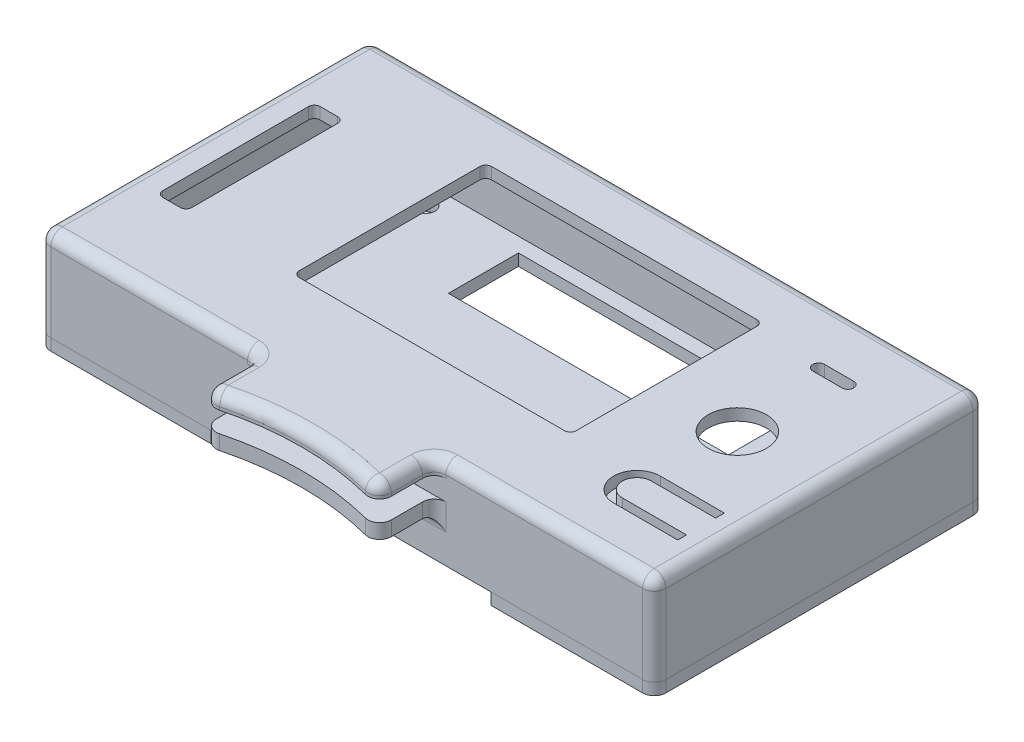
SolidWorks part; units mm, degrees
ref_plane "Alzado" through (0, 0, 0) normal (0, 0, 1) x (1, 0, 0)
ref_plane "Planta" through (0, 0, 0) normal (0, 1, 0) x (1, 0, 0)
ref_plane "Vista lateral" through (0, 0, 0) normal (1, 0, 0) x (0, 0, -1)
sketch "Croquis1" plane through (0, 0, 0) normal (0, 1, 0) x (1, 0, 0)
  line L0 (-2.25, 54.45) -> (103.25, 54.45)
  line L1 (0, 0) -> (101, 0) construction
  line L2 (0, 0) -> (0, 52.2) construction
  line L3 (0, 52.2) -> (101, 52.2) construction
  line L4 (101, 0) -> (101, 52.2) construction
  line L5 (26.6, 45.5) -> (74.1, 45.5)
  line L6 (26.6, 45.5) -> (26.6, 12.5)
  line L7 (26.6, 12.5) -> (74.1, 12.5)
  line L8 (74.1, 45.5) -> (74.1, 12.5)
  line L9 (3, 39.7) -> (8, 39.7)
  line L10 (3, 39.7) -> (3, 12.7)
  line L11 (3, 12.7) -> (8, 12.7)
  line L12 (8, 39.7) -> (8, 12.7)
  line L13 (103.25, -2.25) -> (103.25, 54.45)
  line L14 (-2.25, -2.25) -> (103.25, -2.25)
  line L15 (-2.25, -2.25) -> (-2.25, 54.45)
  line L16 (88.05, 12.48) -> (99.05, 12.48)
  line L17 (88.05, 7.48) -> (99.05, 7.48)
  line L18 (88.05, 5.98) -> (99.05, 5.98)
  line L19 (88.05, 13.98) -> (99.05, 13.98)
  line L20 (99.05, 13.98) -> (99.05, 12.48)
  line L21 (99.05, 7.48) -> (99.05, 5.98)
  line L22 (90.55, 43.65) -> (85.55, 43.65) construction
  line L23 (90.55, 42.65) -> (85.55, 42.65)
  line L24 (90.55, 44.65) -> (85.55, 44.65)
  line L25 (-0.75, -0.75) -> (101.75, -0.75) construction
  line L26 (101.75, -0.75) -> (101.75, 52.95) construction
  line L27 (-0.75, 52.95) -> (101.75, 52.95) construction
  line L28 (-0.75, -0.75) -> (-0.75, 52.95) construction
  circle A0 centre (98.3, 49.5) radius 1.6 construction
  circle A1 centre (98.3, 2.7) radius 1.6 construction
  circle A2 centre (12.3, 49.5) radius 1.6 construction
  circle A3 centre (12.3, 2.7) radius 1.6 construction
  circle A4 centre (88.05, 27.2) radius 5
  circle A5 centre (88.05, 43.65) radius 3 construction
  arc A6 (88.05, 12.48) -> (88.05, 7.48) centre (88.05, 9.98) ccw
  arc A7 (88.05, 13.98) -> (88.05, 5.98) centre (88.05, 9.98) ccw
  arc A8 (90.55, 42.65) -> (90.55, 44.65) centre (90.55, 43.65) ccw
  arc A9 (85.55, 44.65) -> (85.55, 42.65) centre (85.55, 43.65) ccw
  point P41 (88.05, 43.65)
  dimension "D3" = 3.2
  dimension "D6" = 2.7
  dimension "D12" = 10
  dimension "D15" = 6
  dimension "D17" = 5
  dimension "D1" = 52.2
  dimension "D2" = 101
  dimension "D4" = 46.8
  dimension "D5" = 2.7
  dimension "D7" = 86
  dimension "D8" = 47.5
  dimension "D9" = 33
  dimension "D10" = 12.5
  dimension "D11" = 26.9
  dimension "D13" = 12.95
  dimension "D14" = 25
  dimension "D16" = 8.55
  dimension "D18" = 17.22
  dimension "D19" = 27
  dimension "D20" = 5
  dimension "D21" = 12.5
  dimension "D22" = 8
  dimension "D24" = 11
  dimension "D25" = 1.5
  dimension "D26" = 5
  dimension "D27" = 2
  dimension "D23" = 1.5
  dimension "D28" = 0.75
extrude "Saliente-Extruir1" add sketch "Croquis1" along normal blind 2
sketch "Croquis5" plane through (0, 0, 0) normal (0, -1, 0) x (1, 0, 0)
  line L8 (-2.25, 2.25) -> (-2.25, -54.45) construction
  line L9 (-2.25, 2.25) -> (103.25, 2.25) construction
  line L10 (103.25, 2.25) -> (103.25, -54.45) construction
  line L11 (-2.25, -54.45) -> (103.25, -54.45) construction
  line L12 (-2.25, 2.25) -> (-2.25, -54.45)
  line L13 (-2.25, 2.25) -> (103.25, 2.25)
  line L14 (103.25, 2.25) -> (103.25, -54.45)
  line L15 (-2.25, -54.45) -> (103.25, -54.45)
  line L16 (101.75, 0.75) -> (101.75, -52.95) construction
  line L17 (-0.75, 0.75) -> (101.75, 0.75) construction
  line L18 (-0.75, 0.75) -> (-0.75, -52.95) construction
  line L19 (-0.75, -52.95) -> (101.75, -52.95) construction
  line L20 (101.75, 0.75) -> (101.75, -52.95)
  line L21 (-0.75, 0.75) -> (101.75, 0.75)
  line L22 (-0.75, 0.75) -> (-0.75, -52.95)
  line L23 (-0.75, -52.95) -> (101.75, -52.95)
extrude "Saliente-Extruir4" add sketch "Croquis5" along normal blind 13.5
sketch "Croquis6" plane through (0, -13.5, 0) normal (0, -1, 0) x (1, 0, 0)
  line L0 (103.25, 2.25) -> (103.25, -54.45) construction
  line L1 (-2.25, 2.25) -> (103.25, 2.25) construction
  line L2 (-2.25, 2.25) -> (-2.25, -54.45) construction
  line L3 (-2.25, -54.45) -> (103.25, -54.45) construction
  line L4 (103.25, 2.25) -> (103.25, -54.45)
  line L5 (-2.25, 2.25) -> (27.25, 2.25)
  line L6 (-2.25, 2.25) -> (-2.25, -54.45)
  line L7 (-2.25, -54.45) -> (103.25, -54.45)
  line L8 (50.5, 2.25) -> (50.5, -54.45) construction
  line L9 (-0.75, 0.75) -> (-0.75, -52.95) construction
  line L14 (9.45, -48.95) -> (2.45, -48.95)
  line L15 (9.45, -48.95) -> (9.45, -3.95)
  line L16 (9.45, -3.95) -> (2.45, -3.95)
  line L17 (2.45, -48.95) -> (2.45, -3.95)
  line L18 (-0.75, -52.95) -> (101.75, -52.95) construction
  line L19 (103.25, -26.1) -> (-2.25, -26.1) construction
  line L20 (75.25, -50.45) -> (27.25, -50.45)
  line L21 (75.25, -50.45) -> (75.25, -38.45)
  line L22 (75.25, -38.45) -> (27.25, -38.45)
  line L23 (27.25, -50.45) -> (27.25, -38.45)
  line L25 (75.25, 2.25) -> (75.25, -3.75)
  line L26 (75.25, -3.75) -> (27.25, -3.75)
  line L27 (27.25, 2.25) -> (27.25, -3.75)
  line L28 (75.25, 2.25) -> (103.25, 2.25)
  circle A0 centre (98.3, -2.7) radius 1.6 construction
  circle A1 centre (12.3, -49.5) radius 1.6 construction
  circle A2 centre (12.3, -49.5) radius 1.6
  circle A3 centre (98.3, -49.5) radius 1.6 construction
  circle A4 centre (98.3, -2.7) radius 1.6
  circle A7 centre (98.3, -49.5) radius 1.6
  circle A14 centre (12.3, -2.7) radius 1.6 construction
  circle A15 centre (12.3, -2.7) radius 1.6
  circle A16 centre (80.5, -26.1) radius 1.55
  circle A17 centre (20.5, -26.1) radius 1.55
  dimension "D5" = 48
  dimension "D11" = 3.1
  dimension "D1" = 45
  dimension "D2" = 7
  dimension "D3" = 3.2
  dimension "D4" = 4
  dimension "D6" = 12
  dimension "D7" = 2.5
  dimension "D8" = 28
  dimension "D9" = 48
  dimension "D10" = 6
  dimension "D12" = 30
extrude "Saliente-Extruir5" add sketch "Croquis6" along normal blind 2
ref_plane "Plano1" through (0, -13.5, 0) normal (0, -1, 0) x (-1, 0, 0)
sketch "Croquis8" plane through (0, 0, 0) normal (0, -1, 0) x (1, 0, 0)
  line L0 (0, 0) -> (101, 0) construction
  line L2 (9.225, 0.75) -> (9.225, -6.25)
  line L3 (9.225, -6.25) -> (15.375, -6.25)
  line L4 (15.375, 0.75) -> (15.375, -6.25)
  line L5 (101, -26.1) -> (-2.25, -26.1) construction
  line L6 (101, 0) -> (101, -52.2) construction
  line L7 (-2.25, 2.25) -> (-2.25, -54.45) construction
  line L8 (50.5, 0) -> (50.5, -52.2) construction
  line L9 (0, -52.2) -> (101, -52.2) construction
  line L17 (101.75, -6.25) -> (95.6, -6.25)
  line L18 (95.6, 0.75) -> (95.6, -6.25)
  line L23 (101.75, 0.75) -> (101.75, -52.95) construction
  line L24 (-0.75, 0.75) -> (101.75, 0.75) construction
  line L25 (95.6, 0.75) -> (101.75, 0.75)
  line L26 (101.75, 0.75) -> (101.75, -6.25)
  line L27 (9.225, 0.75) -> (15.375, 0.75)
  line L28 (9.225, -52.95) -> (15.375, -52.95)
  line L29 (15.375, -52.95) -> (15.375, -45.95)
  line L30 (9.225, -45.95) -> (15.375, -45.95)
  line L31 (9.225, -52.95) -> (9.225, -45.95)
  line L32 (101.75, -52.95) -> (101.75, -45.95)
  line L33 (95.6, -52.95) -> (101.75, -52.95)
  line L34 (101.75, -45.95) -> (95.6, -45.95)
  line L35 (95.6, -52.95) -> (95.6, -45.95)
  dimension "D1" = 6.15
  dimension "D2" = 7
  dimension "D3" = 3.075
  dimension "D4" = 7
  dimension "D5" = 6.15
extrude "Saliente-Extruir13" add sketch "Croquis8" along normal blind 9
sketch "Croquis9" plane through (0, -9, 0) normal (0, -1, 0) x (1, 0, 0)
  circle A0 centre (12.3, -2.7) radius 2.15
  circle A1 centre (98.3, -2.7) radius 2.15
  circle A2 centre (98.3, -49.5) radius 2.15
  circle A3 centre (12.3, -49.5) radius 2.15
  dimension "D1" = 4.3
extrude "Cortar-Extruir2" cut sketch "Croquis9" against normal blind 3.5
split "Partir1" trim tools "Plano1" bodies to split 108 resulting bodies 111 112
fillet "Redondeo6" radius 1 8 edges at (8, 1, -39.7) (3, 1, -39.7) (3, 1, -12.7) (8, 1, -12.7) (26.6, 1, -12.5) (74.1, 1, -12.5) (74.1, 1, -45.5) (26.6, 1, -45.5)
fillet "Redondeo7" radius 1 18 edges at (101.75, -4.5, -6.25) (100.4, 0, -6.25) (95.6, 0, -2.615) (95.6, -4.5, 0.75) (9.225, -4.5, 0.75) (9.225, 0, -2.75) (12.3, 0, -6.25) (15.375, 0, -2.75) (15.375, -4.5, 0.75) (9.225, -4.5, -52.95) (9.225, 0, -49.45) (12.3, 0, -45.95) (15.375, 0, -49.45) (15.375, -4.5, -52.95) (95.6, -4.5, -52.95) (101.75, -4.5, -45.95) (98.675, 0, -45.95) (95.6, 0, -49.45)
sketch "Croquis10" plane through (0, 0, 0) normal (0, -1, 0) x (1, 0, 0)
  circle A0 centre (88.05, -9.98) radius 2.5
extrude "Saliente-Extruir14" add sketch "Croquis10" along normal blind 2 contours A0
sketch "Croquis13" plane through (0, 0, 2.25) normal (0, 0, 1) x (1, 0, 0)
  line L0 (50.5, 2) -> (50.5, -13.5) construction
  line L1 (-2.25, 2) -> (103.25, 2) construction
  line L2 (103.25, -13.5) -> (-2.25, -13.5) construction
  line L4 (35.5, 2) -> (65.5, 2)
  line L5 (35.5, 2) -> (35.5, -0.5)
  line L6 (35.5, -0.5) -> (65.5, -0.5)
  line L7 (65.5, 2) -> (65.5, -0.5)
  line L8 (35.5, -4) -> (65.5, -4)
  line L9 (35.5, -4) -> (35.5, -6.5)
  line L10 (35.5, -6.5) -> (65.5, -6.5)
  line L11 (65.5, -4) -> (65.5, -6.5)
  dimension "D1" = 30
  dimension "D2" = 2.5
  dimension "D3" = 15
  dimension "D4" = 2.5
  dimension "D5" = 30
  dimension "D6" = 15
  dimension "D7" = 3.5
extrude "Saliente-Extruir16" add sketch "Croquis13" along normal blind 10
sketch "Croquis14" plane through (0, 2, 0) normal (0, 1, 0) x (1, 0, 0)
  line L0 (65.5, -12.25) -> (35.5, -12.25) construction
  line L1 (65.5, -12.25) -> (35.5, -12.25)
  arc A0 (35.5, -12.25) -> (65.5, -12.25) centre (50.5, -59.947) cw
  dimension "D1" = 50
extrude "Cortar-Extruir3" cut sketch "Croquis14" against normal up to surface (8.5 mm away) up to face at (50.5, -6.5, 7.25)
fillet "Redondeo8" radius 2 21 edges at (84.375, 2, 2.25) (35.5, 0.75, 2.25) (35.5, 2, 7.25) (65.5, 0.75, 2.25) (65.5, 2, 7.25) (35.5, 0.75, 12.25) (65.5, 0.75, 12.25) (35.5, -5.25, 2.25) (50.5, -6.5, 2.25) (65.5, -5.25, 2.25) (35.5, -5.25, 12.25) (65.5, -5.25, 12.25) (50.5, 2, 9.947) (-2.25, 2, -26.1) (16.625, 2, 2.25) (103.25, 2, -26.1) (50.5, 2, -54.45) (-2.25, -5.75, -54.45) (103.25, -5.75, -54.45) (103.25, -5.75, 2.25) (-2.25, -5.75, 2.25)
fillet "Redondeo9" radius 2 4 edges at (103.25, -14.5, -54.45) (-2.25, -14.5, -54.45) (103.25, -14.5, 2.25) (-2.25, -14.5, 2.25)
